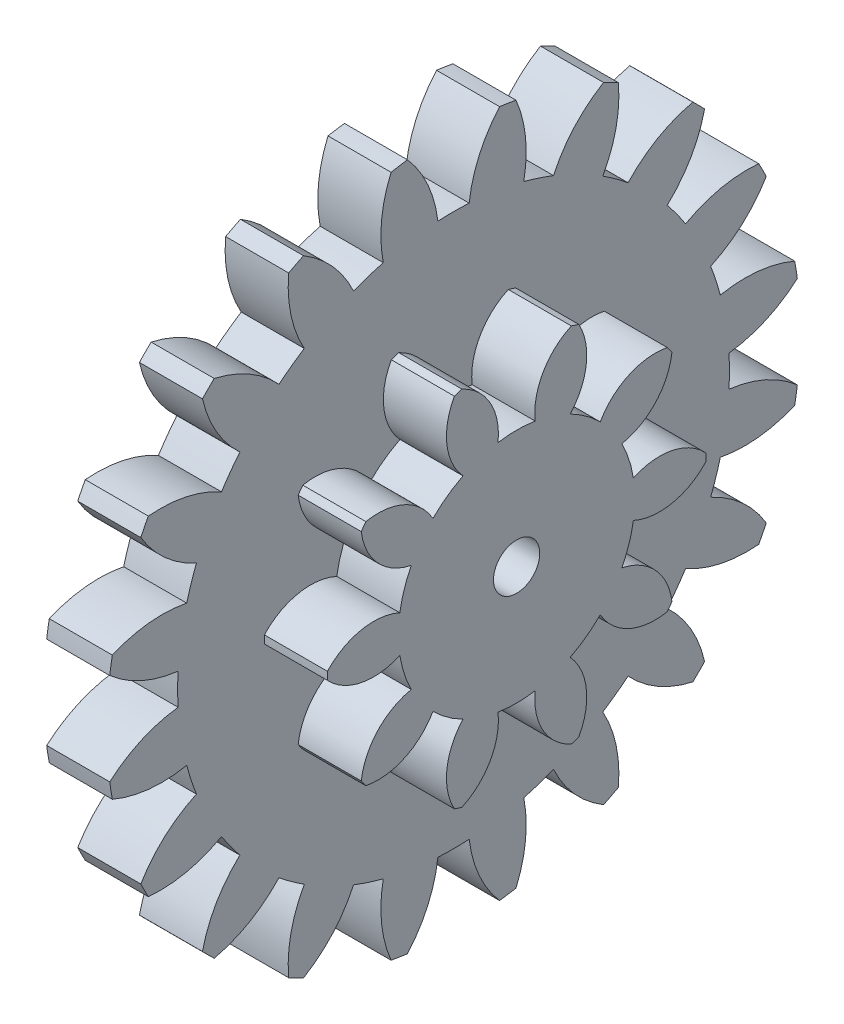
SolidWorks part; units mm, degrees
ref_plane "Front" through (0, 0, 0) normal (0, 0, 1) x (1, 0, 0)
ref_plane "Top" through (0, 0, 0) normal (0, 1, 0) x (1, 0, 0)
ref_plane "Right" through (0, 0, 0) normal (1, 0, 0) x (0, 0, -1)
ref_plane "Plane1" through (0, 0, 4.8986) normal (0, 0, -1) x (-1, 0, 0)
sketch "Sketch1" plane through (0, 0, 4.8986) normal (0, 0, -1) x (-1, 0, 0)
  line L0 (9.1671, 18.2688) -> (9.1671, 1.7688)
  line L1 (9.1671, 1.7688) -> (12.1671, 1.7688)
  line L2 (12.1671, 1.7688) -> (12.1671, 18.2688)
  line L3 (12.1671, 18.2688) -> (9.1671, 18.2688)
  line L4 (9.1671, 1.7688) -> (12.1671, 1.7688) construction
revolve "Revolve1" add sketch "Sketch1" angle 360 about L4
sketch "Sketch2" plane through (-12.1671, 0, 0) normal (-1, 0, 0) x (0, 0, 1)
  arc A0 (-11.4554, 3.9586) -> (-11.4554, -0.4209) centre (4.8986, 1.7688) ccw
  arc A1 (-11.4554, -0.4209) -> (-8.2043, 1.025) centre (-7.5013, -4.9336) cw
  arc A2 (-8.2043, 1.025) -> (-8.2043, 2.5126) centre (4.8986, 1.7688) cw
  arc A3 (-8.2043, 2.5126) -> (-11.4554, 3.9586) centre (-7.5013, 8.4713) cw
extrude "Cut-Extrude1" cut sketch "Sketch2" against normal through all
sketch "Sketch3" plane through (-12.1671, 0, 0) normal (-1, 0, 0) x (0, 0, 1)
  arc A0 (-9.9783, 8.9051) -> (-11.3317, 4.7399) centre (4.8986, 1.7688) ccw
  arc A1 (-11.3317, 4.7399) -> (-7.7929, 5.1104) centre (-8.9656, -0.7738) cw
  arc A2 (-7.7929, 5.1104) -> (-7.3332, 6.5253) centre (4.8986, 1.7688) cw
  arc A3 (-7.3332, 6.5253) -> (-9.9783, 8.9051) centre (-4.8232, 11.975) cw
extrude "Cut-Extrude2" cut sketch "Sketch3" against normal through all
sketch "Sketch4" plane through (-12.1671, 0, 0) normal (-1, 0, 0) x (0, 0, 1)
  arc A0 (-7.045, 13.1531) -> (-9.6192, 9.6099) centre (4.8986, 1.7688) ccw
  arc A1 (-9.6192, 9.6099) -> (-6.1391, 8.8688) centre (-9.0727, 3.6349) cw
  arc A2 (-6.1391, 8.8688) -> (-5.2647, 10.0723) centre (4.8986, 1.7688) cw
  arc A3 (-5.2647, 10.0723) -> (-7.045, 13.1531) centre (-1.1935, 14.4797) cw
extrude "Cut-Extrude3" cut sketch "Sketch4" against normal through all
sketch "Sketch5" plane through (-12.1671, 0, 0) normal (-1, 0, 0) x (0, 0, 1)
  arc A0 (-2.9425, 16.2867) -> (-6.4856, 13.7124) centre (4.8986, 1.7688) ccw
  arc A1 (-6.4856, 13.7124) -> (-3.4049, 11.9321) centre (-7.8123, 7.8609) cw
  arc A2 (-3.4049, 11.9321) -> (-2.2013, 12.8065) centre (4.8986, 1.7688) cw
  arc A3 (-2.2013, 12.8065) -> (-2.9425, 16.2867) centre (3.0326, 15.7402) cw
extrude "Cut-Extrude4" cut sketch "Sketch5" against normal through all
sketch "Sketch6" plane through (-12.1671, 0, 0) normal (-1, 0, 0) x (0, 0, 1)
  arc A0 (1.9275, 17.9991) -> (-2.2377, 16.6458) centre (4.8986, 1.7688) ccw
  arc A1 (-2.2377, 16.6458) -> (0.1422, 14.0006) centre (-5.3076, 11.4906) cw
  arc A2 (0.1422, 14.0006) -> (1.557, 14.4603) centre (4.8986, 1.7688) cw
  arc A3 (1.557, 14.4603) -> (1.9275, 17.9991) centre (7.4413, 15.633) cw
extrude "Cut-Extrude5" cut sketch "Sketch6" against normal through all
sketch "Sketch7" plane through (-12.1671, 0, 0) normal (-1, 0, 0) x (0, 0, 1)
  arc A0 (7.0884, 18.1229) -> (2.7088, 18.1229) centre (4.8986, 1.7688) ccw
  arc A1 (2.7088, 18.1229) -> (4.1548, 14.8717) centre (-1.8039, 14.1687) cw
  arc A2 (4.1548, 14.8717) -> (5.6424, 14.8717) centre (4.8986, 1.7688) cw
  arc A3 (5.6424, 14.8717) -> (7.0884, 18.1229) centre (11.6011, 14.1687) cw
extrude "Cut-Extrude6" cut sketch "Sketch7" against normal through all
sketch "Sketch8" plane through (-12.1671, 0, 0) normal (-1, 0, 0) x (0, 0, 1)
  arc A0 (12.0349, 16.6458) -> (7.8697, 17.9991) centre (4.8986, 1.7688) ccw
  arc A1 (7.8697, 17.9991) -> (8.2402, 14.4603) centre (2.3559, 15.633) cw
  arc A2 (8.2402, 14.4603) -> (9.655, 14.0006) centre (4.8986, 1.7688) cw
  arc A3 (9.655, 14.0006) -> (12.0349, 16.6458) centre (15.1048, 11.4906) cw
extrude "Cut-Extrude7" cut sketch "Sketch8" against normal through all
sketch "Sketch9" plane through (-12.1671, 0, 0) normal (-1, 0, 0) x (0, 0, 1)
  arc A0 (16.2828, 13.7124) -> (12.7397, 16.2867) centre (4.8986, 1.7688) ccw
  arc A1 (12.7397, 16.2867) -> (11.9985, 12.8065) centre (6.7646, 15.7402) cw
  arc A2 (11.9985, 12.8065) -> (13.2021, 11.9321) centre (4.8986, 1.7688) cw
  arc A3 (13.2021, 11.9321) -> (16.2828, 13.7124) centre (17.6095, 7.8609) cw
extrude "Cut-Extrude8" cut sketch "Sketch9" against normal through all
sketch "Sketch10" plane through (-12.1671, 0, 0) normal (-1, 0, 0) x (0, 0, 1)
  arc A0 (19.4164, 9.6099) -> (16.8422, 13.1531) centre (4.8986, 1.7688) ccw
  arc A1 (16.8422, 13.1531) -> (15.0619, 10.0723) centre (10.9907, 14.4797) cw
  arc A2 (15.0619, 10.0723) -> (15.9363, 8.8688) centre (4.8986, 1.7688) cw
  arc A3 (15.9363, 8.8688) -> (19.4164, 9.6099) centre (18.8699, 3.6349) cw
extrude "Cut-Extrude9" cut sketch "Sketch10" against normal through all
sketch "Sketch11" plane through (-12.1671, 0, 0) normal (-1, 0, 0) x (0, 0, 1)
  arc A0 (21.1289, 4.7399) -> (19.7755, 8.9051) centre (4.8986, 1.7688) ccw
  arc A1 (19.7755, 8.9051) -> (17.1304, 6.5253) centre (14.6204, 11.975) cw
  arc A2 (17.1304, 6.5253) -> (17.5901, 5.1104) centre (4.8986, 1.7688) cw
  arc A3 (17.5901, 5.1104) -> (21.1289, 4.7399) centre (18.7628, -0.7738) cw
extrude "Cut-Extrude10" cut sketch "Sketch11" against normal through all
sketch "Sketch12" plane through (-12.1671, 0, 0) normal (-1, 0, 0) x (0, 0, 1)
  arc A0 (21.2526, -0.4209) -> (21.2526, 3.9586) centre (4.8986, 1.7688) ccw
  arc A1 (21.2526, 3.9586) -> (18.0015, 2.5126) centre (17.2985, 8.4713) cw
  arc A2 (18.0015, 2.5126) -> (18.0015, 1.025) centre (4.8986, 1.7688) cw
  arc A3 (18.0015, 1.025) -> (21.2526, -0.4209) centre (17.2985, -4.9336) cw
extrude "Cut-Extrude11" cut sketch "Sketch12" against normal through all
sketch "Sketch13" plane through (-12.1671, 0, 0) normal (-1, 0, 0) x (0, 0, 1)
  arc A0 (19.7755, -5.3675) -> (21.1289, -1.2022) centre (4.8986, 1.7688) ccw
  arc A1 (21.1289, -1.2022) -> (17.5901, -1.5728) centre (18.7628, 4.3115) cw
  arc A2 (17.5901, -1.5728) -> (17.1304, -2.9876) centre (4.8986, 1.7688) cw
  arc A3 (17.1304, -2.9876) -> (19.7755, -5.3675) centre (14.6204, -8.4374) cw
extrude "Cut-Extrude12" cut sketch "Sketch13" against normal through all
sketch "Sketch14" plane through (-12.1671, 0, 0) normal (-1, 0, 0) x (0, 0, 1)
  arc A0 (16.8422, -9.6154) -> (19.4164, -6.0723) centre (4.8986, 1.7688) ccw
  arc A1 (19.4164, -6.0723) -> (15.9363, -5.3311) centre (18.8699, -0.0972) cw
  arc A2 (15.9363, -5.3311) -> (15.0619, -6.5346) centre (4.8986, 1.7688) cw
  arc A3 (15.0619, -6.5346) -> (16.8422, -9.6154) centre (10.9907, -10.942) cw
extrude "Cut-Extrude13" cut sketch "Sketch14" against normal through all
sketch "Sketch15" plane through (-12.1671, 0, 0) normal (-1, 0, 0) x (0, 0, 1)
  arc A0 (12.7397, -12.749) -> (16.2828, -10.1747) centre (4.8986, 1.7688) ccw
  arc A1 (16.2828, -10.1747) -> (13.2021, -8.3944) centre (17.6095, -4.3232) cw
  arc A2 (13.2021, -8.3944) -> (11.9985, -9.2688) centre (4.8986, 1.7688) cw
  arc A3 (11.9985, -9.2688) -> (12.7397, -12.749) centre (6.7646, -12.2025) cw
extrude "Cut-Extrude14" cut sketch "Sketch15" against normal through all
sketch "Sketch16" plane through (-12.1671, 0, 0) normal (-1, 0, 0) x (0, 0, 1)
  arc A0 (7.8697, -14.4615) -> (12.0349, -13.1081) centre (4.8986, 1.7688) ccw
  arc A1 (12.0349, -13.1081) -> (9.655, -10.4629) centre (15.1048, -7.953) cw
  arc A2 (9.655, -10.4629) -> (8.2402, -10.9226) centre (4.8986, 1.7688) cw
  arc A3 (8.2402, -10.9226) -> (7.8697, -14.4615) centre (2.3559, -12.0953) cw
extrude "Cut-Extrude15" cut sketch "Sketch16" against normal through all
sketch "Sketch17" plane through (-12.1671, 0, 0) normal (-1, 0, 0) x (0, 0, 1)
  arc A0 (2.7088, -14.5852) -> (7.0884, -14.5852) centre (4.8986, 1.7688) ccw
  arc A1 (7.0884, -14.5852) -> (5.6424, -11.3341) centre (11.6011, -10.631) cw
  arc A2 (5.6424, -11.3341) -> (4.1548, -11.3341) centre (4.8986, 1.7688) cw
  arc A3 (4.1548, -11.3341) -> (2.7088, -14.5852) centre (-1.8039, -10.631) cw
extrude "Cut-Extrude16" cut sketch "Sketch17" against normal through all
sketch "Sketch18" plane through (-12.1671, 0, 0) normal (-1, 0, 0) x (0, 0, 1)
  arc A0 (-2.2377, -13.1081) -> (1.9275, -14.4615) centre (4.8986, 1.7688) ccw
  arc A1 (1.9275, -14.4615) -> (1.557, -10.9226) centre (7.4413, -12.0953) cw
  arc A2 (1.557, -10.9226) -> (0.1422, -10.4629) centre (4.8986, 1.7688) cw
  arc A3 (0.1422, -10.4629) -> (-2.2377, -13.1081) centre (-5.3076, -7.953) cw
extrude "Cut-Extrude17" cut sketch "Sketch18" against normal through all
sketch "Sketch19" plane through (-12.1671, 0, 0) normal (-1, 0, 0) x (0, 0, 1)
  arc A0 (-6.4856, -10.1747) -> (-2.9425, -12.749) centre (4.8986, 1.7688) ccw
  arc A1 (-2.9425, -12.749) -> (-2.2013, -9.2688) centre (3.0326, -12.2025) cw
  arc A2 (-2.2013, -9.2688) -> (-3.4049, -8.3944) centre (4.8986, 1.7688) cw
  arc A3 (-3.4049, -8.3944) -> (-6.4856, -10.1747) centre (-7.8123, -4.3232) cw
extrude "Cut-Extrude18" cut sketch "Sketch19" against normal through all
sketch "Sketch20" plane through (-12.1671, 0, 0) normal (-1, 0, 0) x (0, 0, 1)
  arc A0 (-9.6192, -6.0723) -> (-7.045, -9.6154) centre (4.8986, 1.7688) ccw
  arc A1 (-7.045, -9.6154) -> (-5.2647, -6.5346) centre (-1.1935, -10.942) cw
  arc A2 (-5.2647, -6.5346) -> (-6.1391, -5.3311) centre (4.8986, 1.7688) cw
  arc A3 (-6.1391, -5.3311) -> (-9.6192, -6.0723) centre (-9.0727, -0.0972) cw
extrude "Cut-Extrude19" cut sketch "Sketch20" against normal through all
sketch "Sketch21" plane through (-12.1671, 0, 0) normal (-1, 0, 0) x (0, 0, 1)
  arc A0 (-11.3317, -1.2022) -> (-9.9783, -5.3675) centre (4.8986, 1.7688) ccw
  arc A1 (-9.9783, -5.3675) -> (-7.3332, -2.9876) centre (-4.8232, -8.4374) cw
  arc A2 (-7.3332, -2.9876) -> (-7.7929, -1.5728) centre (4.8986, 1.7688) cw
  arc A3 (-7.7929, -1.5728) -> (-11.3317, -1.2022) centre (-8.9656, 4.3115) cw
extrude "Cut-Extrude20" cut sketch "Sketch21" against normal through all
sketch "Sketch22" plane through (-9.1671, 0, 0) normal (1, 0, 0) x (0, 0, -1)
  arc A0 (-9.9077, -0.7881) -> (-10.454, 0.8931) centre (-4.8986, 1.7688) cw
  arc A1 (-10.454, 0.8931) -> (-13.8967, 1.582) centre (-11.698, 3.6231) cw
  arc A2 (-13.8967, 1.582) -> (-13.8967, 1.9557) centre (-4.8986, 1.7688) cw
  arc A3 (-13.8967, 1.9557) -> (-10.454, 2.6445) centre (-11.698, -0.0854) cw
  arc A4 (-10.454, 2.6445) -> (-9.9077, 4.3258) centre (-4.8986, 1.7688) cw
  arc A5 (-9.9077, 4.3258) -> (-12.288, 6.9066) centre (-9.3095, 7.2655) cw
  arc A6 (-12.288, 6.9066) -> (-12.0684, 7.2089) centre (-4.8986, 1.7688) cw
  arc A7 (-12.0684, 7.2089) -> (-8.8783, 5.7427) centre (-11.4893, 4.2653) cw
  arc A8 (-8.8783, 5.7427) -> (-7.4481, 6.7817) centre (-4.8986, 1.7688) cw
  arc A9 (-7.4481, 6.7817) -> (-7.8568, 10.2688) centre (-5.2363, 8.8084) cw
  arc A10 (-7.8568, 10.2688) -> (-7.5015, 10.3842) centre (-4.8986, 1.7688) cw
  arc A11 (-7.5015, 10.3842) -> (-5.7825, 7.3229) centre (-8.7632, 7.6625) cw
  arc A12 (-5.7825, 7.3229) -> (-4.0147, 7.3229) centre (-4.8986, 1.7688) cw
  arc A13 (-4.0147, 7.3229) -> (-2.2957, 10.3842) centre (-1.034, 7.6625) cw
  arc A14 (-2.2957, 10.3842) -> (-1.9404, 10.2688) centre (-4.8986, 1.7688) cw
  arc A15 (-1.9404, 10.2688) -> (-2.349, 6.7817) centre (-4.5609, 8.8084) cw
  arc A16 (-2.349, 6.7817) -> (-0.9189, 5.7427) centre (-4.8986, 1.7688) cw
  arc A17 (-0.9189, 5.7427) -> (2.2712, 7.2089) centre (1.6921, 4.2653) cw
  arc A18 (2.2712, 7.2089) -> (2.4908, 6.9066) centre (-4.8986, 1.7688) cw
  arc A19 (2.4908, 6.9066) -> (0.1105, 4.3258) centre (-0.4877, 7.2655) cw
  arc A20 (0.1105, 4.3258) -> (0.6568, 2.6445) centre (-4.8986, 1.7688) cw
  arc A21 (0.6568, 2.6445) -> (4.0995, 1.9557) centre (1.9008, -0.0854) cw
  arc A22 (4.0995, 1.9557) -> (4.0995, 1.582) centre (-4.8986, 1.7688) cw
  arc A23 (4.0995, 1.582) -> (0.6568, 0.8931) centre (1.9008, 3.6231) cw
  arc A24 (0.6568, 0.8931) -> (0.1105, -0.7881) centre (-4.8986, 1.7688) cw
  arc A25 (0.1105, -0.7881) -> (2.4908, -3.3689) centre (-0.4877, -3.7279) cw
  arc A26 (2.4908, -3.3689) -> (2.2712, -3.6712) centre (-4.8986, 1.7688) cw
  arc A27 (2.2712, -3.6712) -> (-0.9189, -2.205) centre (1.6921, -0.7277) cw
  arc A28 (-0.9189, -2.205) -> (-2.349, -3.2441) centre (-4.8986, 1.7688) cw
  arc A29 (-2.349, -3.2441) -> (-1.9404, -6.7311) centre (-4.5609, -5.2708) cw
  arc A30 (-1.9404, -6.7311) -> (-2.2957, -6.8466) centre (-4.8986, 1.7688) cw
  arc A31 (-2.2957, -6.8466) -> (-4.0147, -3.7853) centre (-1.034, -4.1248) cw
  arc A32 (-4.0147, -3.7853) -> (-5.7825, -3.7853) centre (-4.8986, 1.7688) cw
  arc A33 (-5.7825, -3.7853) -> (-7.5015, -6.8466) centre (-8.7632, -4.1248) cw
  arc A34 (-7.5015, -6.8466) -> (-7.8568, -6.7311) centre (-4.8986, 1.7688) cw
  arc A35 (-7.8568, -6.7311) -> (-7.4481, -3.2441) centre (-5.2363, -5.2708) cw
  arc A36 (-7.4481, -3.2441) -> (-8.8783, -2.205) centre (-4.8986, 1.7688) cw
  arc A37 (-8.8783, -2.205) -> (-12.0684, -3.6712) centre (-11.4893, -0.7277) cw
  arc A38 (-12.0684, -3.6712) -> (-12.288, -3.3689) centre (-4.8986, 1.7688) cw
  arc A39 (-12.288, -3.3689) -> (-9.9077, -0.7881) centre (-9.3095, -3.7279) cw
extrude "Boss-Extrude1" add sketch "Sketch22" along normal blind 3
hole_wizard "Ø2.2 (2.2) Diameter Hole1" positions "Sketch24" profile "Sketch23" hole size "Ø2.2" standard "ANSI Metric"
sketch "Sketch24" plane through (-12.1671, 0, 0) normal (-1, 0, 0) x (0, 0, 1)
  point P0 (4.8986, 1.7688)
sketch "Sketch23" plane through (-12.1671, 1.7688, 4.8986) normal (0, 1, 0) x (0, 0, 1)
  line L0 (0, 0) -> (0, 6)
  line L1 (0, 6) -> (1.1, 6)
  line L2 (1.1, 6) -> (1.1, 0)
  line L5 (1.1, 0) -> (0, 0)
  line L11 (0, -6.35) -> (0, 107.95) construction
  dimension "Thru Hole Dia." = 2.2
  dimension "Thru Hole Depth" = 6
